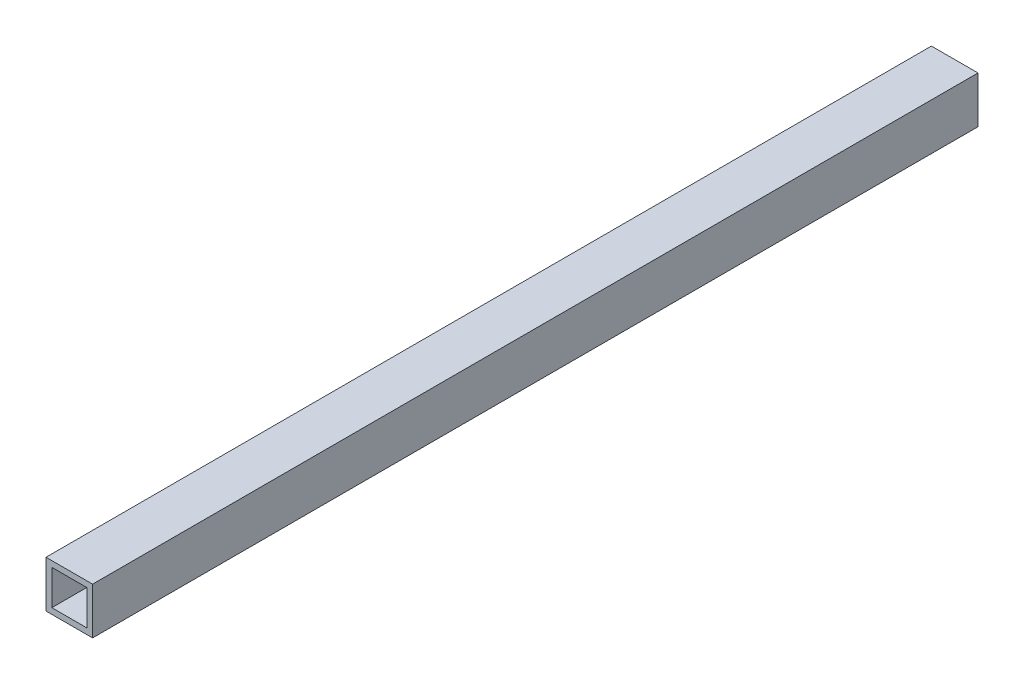
SolidWorks part; units mm, degrees
material "5052-H32"
ref_plane "Front Plane" through (0, 0, 0) normal (0, 0, 1) x (1, 0, 0)
ref_plane "Top Plane" through (0, 0, 0) normal (0, 1, 0) x (1, 0, 0)
ref_plane "Right Plane" through (0, 0, 0) normal (1, 0, 0) x (0, 0, -1)
sketch "Sketch1" plane through (0, 0, 0) normal (0, 0, 1) x (1, 0, 0)
  line L1 (-12.7, -12.7) -> (12.7, -12.7)
  line L2 (-12.7, -12.7) -> (-12.7, 12.7)
  line L3 (-12.7, 12.7) -> (12.7, 12.7)
  line L4 (12.7, -12.7) -> (12.7, 12.7)
  line L5 (-12.7, -12.7) -> (12.7, 12.7) construction
  line L6 (-12.7, 12.7) -> (12.7, -12.7) construction
  line L7 (-9.525, -9.525) -> (9.525, -9.525)
  line L8 (-9.525, -9.525) -> (-9.525, 9.525)
  line L9 (-9.525, 9.525) -> (9.525, 9.525)
  line L10 (9.525, -9.525) -> (9.525, 9.525)
  line L11 (-9.525, -9.525) -> (9.525, 9.525) construction
  line L12 (-9.525, 9.525) -> (9.525, -9.525) construction
  point P0 (0, 0)
  point P6 (0, 0)
  dimension "D1" = 25.4
  dimension "D2" = 3.175
extrude "Boss-Extrude1" add sketch "Sketch1" along normal blind 482.6
